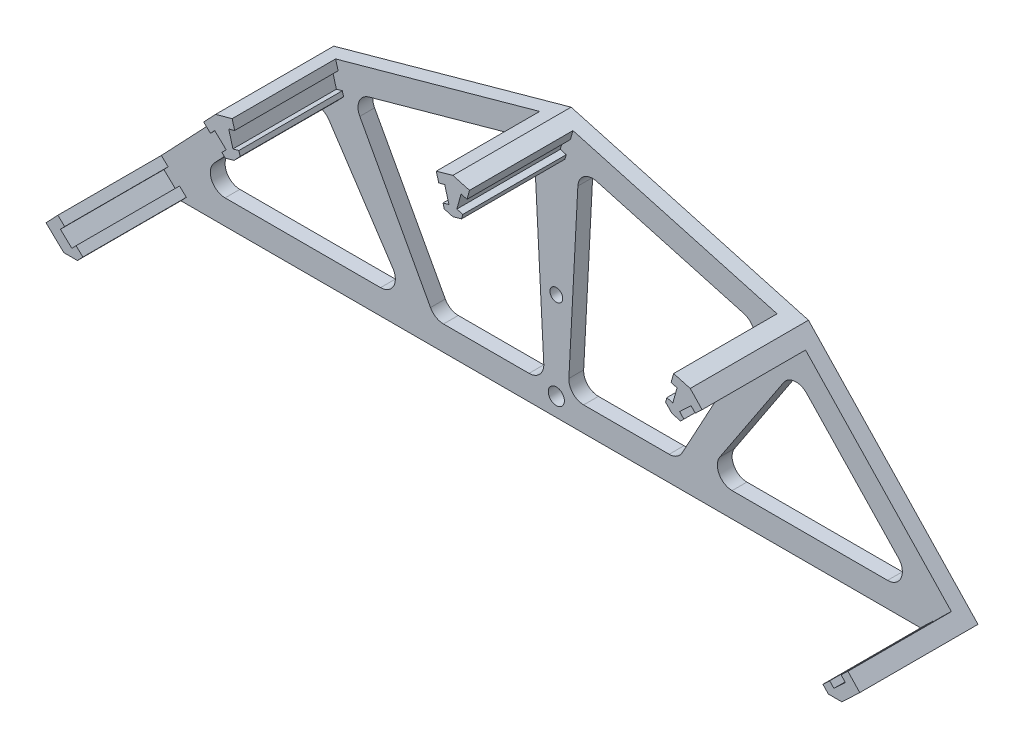
SolidWorks part; units mm, degrees
ref_plane "Front Plane" through (0, 0, 0) normal (0, 0, 1) x (1, 0, 0)
ref_plane "Top Plane" through (0, 0, 0) normal (0, 1, 0) x (1, 0, 0)
ref_plane "Right Plane" through (0, 0, 0) normal (1, 0, 0) x (0, 0, -1)
sketch "Sketch1" plane through (0, 0, 0) normal (0, 0, 1) x (1, 0, 0)
  line L0 (0, -46.7747) -> (0, 46.7747) construction
  line L1 (-82.5993, -2.8559) -> (-78.9724, -6.2977)
  line L2 (82.5993, -2.8559) -> (0, -46.7747) construction
  line L3 (0, 46.7747) -> (48.1815, 33.4128)
  line L4 (48.1815, 33.4128) -> (0, -46.7747) construction
  line L5 (48.1815, 33.4128) -> (82.5993, -2.8559)
  line L6 (82.5993, -2.8559) -> (78.9724, -6.2977)
  line L7 (-48.1815, 33.4128) -> (-82.5993, -2.8559)
  line L8 (-48.1815, 33.4128) -> (0, -46.7747) construction
  line L9 (0, 46.7747) -> (-48.1815, 33.4128)
  line L10 (-82.5993, -2.8559) -> (0, -46.7747) construction
  line L11 (-78.9724, -6.2977) -> (78.9724, -6.2977)
  dimension "D1" = 5
  dimension "D2" = 31
  dimension "D3" = 31
  dimension "D4" = 50
extrude "Boss-Extrude1" add sketch "Sketch1" along normal blind 3
sketch "Sketch2" plane through (0, 0, 3) normal (0, 0, 1) x (1, 0, 0)
  line L0 (-48.1815, 33.4128) -> (-44.8088, 34.3481)
  line L1 (0, 46.7747) -> (-48.1815, 33.4128) construction
  line L2 (-44.8088, 34.3481) -> (-44.3011, 32.5172)
  line L3 (-42.9381, 27.6027) -> (-46.3109, 26.6674)
  line L4 (-46.3109, 26.6674) -> (-48.1815, 33.4128) construction
  line L5 (-5.6614, 41.5726) -> (-1.2328, 42.8007) construction
  line L6 (1.8707, 40.0293) -> (0, 46.7747) construction
  line L7 (-1.502, 39.094) -> (1.8707, 40.0293)
  line L8 (-2.0098, 40.9249) -> (-1.502, 39.094)
  line L9 (-24.0908, 40.0938) -> (-22.238, 33.4128) construction
  line L10 (0, 46.7747) -> (-48.1815, 33.4128) construction
  line L11 (-45.5056, 32.1832) -> (-44.6504, 29.0996)
  line L12 (-44.3011, 32.5172) -> (-45.5056, 32.1832)
  line L13 (-40.6495, 31.8695) -> (-45.078, 30.6414) construction
  line L14 (-43.4459, 29.4336) -> (-44.6504, 29.0996)
  line L15 (-43.4459, 29.4336) -> (-42.9381, 27.6027)
  line L16 (-2.0098, 40.9249) -> (-0.8053, 41.2589)
  line L17 (-2.865, 44.0085) -> (-1.6604, 44.3425)
  line L18 (-1.6604, 44.3425) -> (-0.8053, 41.2589)
  line L19 (-3.3727, 45.8394) -> (-2.865, 44.0085)
  line L20 (0, 46.7747) -> (-3.3727, 45.8394)
  line L21 (0, 46.7747) -> (0, -46.7747) construction
  line L22 (40.6495, 31.8695) -> (45.078, 30.6414) construction
  line L23 (24.0908, 40.0938) -> (22.238, 33.4128) construction
  line L24 (1.502, 39.094) -> (-1.8707, 40.0293)
  line L25 (-1.8707, 40.0293) -> (0, 46.7747) construction
  line L26 (5.6614, 41.5726) -> (1.2328, 42.8007) construction
  line L27 (46.3109, 26.6674) -> (48.1815, 33.4128) construction
  line L28 (42.9381, 27.6027) -> (46.3109, 26.6674)
  line L29 (0, 46.7747) -> (3.3727, 45.8394)
  line L30 (3.3727, 45.8394) -> (2.865, 44.0085)
  line L31 (1.6604, 44.3425) -> (0.8053, 41.2589)
  line L32 (2.865, 44.0085) -> (1.6604, 44.3425)
  line L33 (2.0098, 40.9249) -> (0.8053, 41.2589)
  line L34 (43.4459, 29.4336) -> (42.9381, 27.6027)
  line L35 (43.4459, 29.4336) -> (44.6504, 29.0996)
  line L36 (44.3011, 32.5172) -> (45.5056, 32.1832)
  line L37 (45.5056, 32.1832) -> (44.6504, 29.0996)
  line L38 (2.0098, 40.9249) -> (1.502, 39.094)
  line L39 (44.8088, 34.3481) -> (44.3011, 32.5172)
  line L40 (48.1815, 33.4128) -> (44.8088, 34.3481)
  line L41 (48.1815, 33.4128) -> (0, -46.7747) construction
  line L42 (0, -46.7747) -> (-48.1815, 33.4128) construction
  line L43 (-75.7652, -4.371) -> (-82.5993, -2.8559) construction
  line L44 (-50.355, 26.0379) -> (-47.1915, 29.3715) construction
  line L45 (-65.3904, 15.2784) -> (-60.3613, 10.506) construction
  line L46 (-75.1124, -5.1356) -> (-77.5216, -7.6744)
  line L47 (-77.5216, -7.6744) -> (-82.5993, -2.8559)
  line L48 (-75.3482, -0.2995) -> (-78.5116, -3.6331) construction
  line L49 (-43.1039, 28.5943) -> (-48.1815, 33.4128) construction
  line L50 (-45.5131, 26.0555) -> (-43.1039, 28.5943)
  line L51 (-82.5993, -2.8559) -> (-80.19, -0.3171)
  line L52 (-80.19, -0.3171) -> (-78.8118, -1.625)
  line L53 (-79.6722, -2.5317) -> (-77.351, -4.7344)
  line L54 (-78.8118, -1.625) -> (-79.6722, -2.5317)
  line L55 (-76.4906, -3.8277) -> (-77.351, -4.7344)
  line L56 (-46.8914, 27.3634) -> (-45.5131, 26.0555)
  line L57 (-46.8914, 27.3634) -> (-46.0309, 28.2701)
  line L58 (-49.2126, 29.5661) -> (-48.3521, 30.4728)
  line L59 (-48.3521, 30.4728) -> (-46.0309, 28.2701)
  line L60 (-76.4906, -3.8277) -> (-75.1124, -5.1356)
  line L61 (-50.5908, 30.874) -> (-49.2126, 29.5661)
  line L62 (-48.1815, 33.4128) -> (-50.5908, 30.874)
  line L63 (45.5131, 26.0555) -> (43.1039, 28.5943)
  line L64 (43.1039, 28.5943) -> (48.1815, 33.4128) construction
  line L65 (75.3482, -0.2995) -> (78.5116, -3.6331) construction
  line L66 (77.5216, -7.6744) -> (82.5993, -2.8559)
  line L67 (75.1124, -5.1356) -> (77.5216, -7.6744)
  line L68 (65.3904, 15.2784) -> (60.3613, 10.506) construction
  line L69 (50.355, 26.0379) -> (47.1915, 29.3715) construction
  line L70 (48.1815, 33.4128) -> (50.5908, 30.874)
  line L71 (50.5908, 30.874) -> (49.2126, 29.5661)
  line L72 (76.4906, -3.8277) -> (75.1124, -5.1356)
  line L73 (48.3521, 30.4728) -> (46.0309, 28.2701)
  line L74 (49.2126, 29.5661) -> (48.3521, 30.4728)
  line L75 (46.8914, 27.3634) -> (46.0309, 28.2701)
  line L76 (46.8914, 27.3634) -> (45.5131, 26.0555)
  line L77 (76.4906, -3.8277) -> (77.351, -4.7344)
  line L78 (78.8118, -1.625) -> (79.6722, -2.5317)
  line L79 (79.6722, -2.5317) -> (77.351, -4.7344)
  line L80 (80.19, -0.3171) -> (78.8118, -1.625)
  line L81 (82.5993, -2.8559) -> (80.19, -0.3171)
  line L82 (-40.6495, 31.8695) -> (-47.2462, 30.0401) construction
  point P20 (-40.7831, 32.3513)
  point P94 (-47.2462, 30.0401)
  point P98 (-40.6268, 31.7304)
  dimension "D1" = 7
  dimension "D2" = 22.75
  dimension "D3" = 1.6
  dimension "D4" = 1.25
extrude "Boss-Extrude2" add sketch "Sketch2" along normal blind 21
sketch "Sketch3" plane through (0, 0, 3) normal (0, 0, 1) x (1, 0, 0)
  line L0 (0, -46.7747) -> (-74.2276, -1.2977) construction
  line L1 (-69.421, 3.7674) -> (-50.8282, 23.3601)
  line L2 (-46.1504, 22.9509) -> (-33.1822, 3.3581)
  line L3 (-35.6839, -1.2977) -> (-67.2449, -1.2977)
  line L4 (-25.5437, 0.2708) -> (-39.8978, 26.7078)
  line L5 (-38.063, 31.0302) -> (-8.1664, 39.3213)
  line L6 (-4.3688, 36.5874) -> (-2.5488, 1.8593)
  line L7 (-5.5447, -1.2977) -> (-22.9072, -1.2977)
  line L8 (-48.1815, 33.4128) -> (-82.5993, -2.8559) construction
  line L9 (0, 46.7747) -> (-48.1815, 33.4128) construction
  line L10 (-78.9724, -6.2977) -> (78.9724, -6.2977) construction
  line L11 (-48.1815, 33.4128) -> (0, -46.7747) construction
  line L12 (0, -46.7747) -> (0, 46.7747) construction
  line L13 (-2.5488, 1.8593) -> (0, -46.7747) construction
  line L14 (0, 46.7747) -> (0, 0) construction
  line L15 (5.5447, -1.2977) -> (22.9072, -1.2977)
  line L16 (4.3688, 36.5874) -> (2.5488, 1.8593)
  line L17 (38.063, 31.0302) -> (8.1664, 39.3213)
  line L18 (25.5437, 0.2708) -> (39.8978, 26.7078)
  line L19 (35.6839, -1.2977) -> (67.2449, -1.2977)
  line L20 (46.1504, 22.9509) -> (33.1822, 3.3581)
  line L21 (69.421, 3.7674) -> (50.8282, 23.3601)
  arc A0 (-35.6839, -1.2977) -> (-33.1822, 3.3581) centre (-35.6839, 1.7023) ccw
  arc A1 (-50.8282, 23.3601) -> (-46.1504, 22.9509) centre (-48.652, 21.2951) cw
  arc A2 (-69.421, 3.7674) -> (-67.2449, -1.2977) centre (-67.2449, 1.7023) ccw
  arc A3 (-25.5437, 0.2708) -> (-22.9072, -1.2977) centre (-22.9072, 1.7023) ccw
  arc A4 (-39.8978, 26.7078) -> (-38.063, 31.0302) centre (-37.2613, 28.1393) cw
  arc A5 (-8.1664, 39.3213) -> (-4.3688, 36.5874) centre (-7.3647, 36.4304) cw
  arc A6 (-2.5488, 1.8593) -> (-5.5447, -1.2977) centre (-5.5447, 1.7023) cw
  arc A7 (2.5488, 1.8593) -> (5.5447, -1.2977) centre (5.5447, 1.7023) ccw
  arc A8 (8.1664, 39.3213) -> (4.3688, 36.5874) centre (7.3647, 36.4304) ccw
  arc A9 (39.8978, 26.7078) -> (38.063, 31.0302) centre (37.2613, 28.1393) ccw
  arc A10 (25.5437, 0.2708) -> (22.9072, -1.2977) centre (22.9072, 1.7023) cw
  arc A11 (69.421, 3.7674) -> (67.2449, -1.2977) centre (67.2449, 1.7023) cw
  arc A12 (50.8282, 23.3601) -> (46.1504, 22.9509) centre (48.652, 21.2951) ccw
  arc A13 (35.6839, -1.2977) -> (33.1822, 3.3581) centre (35.6839, 1.7023) cw
  circle A14 centre (0, -2.5545) radius 1.6425
  circle A15 centre (0, 15.2704) radius 1.293
  dimension "D6" = 3
  dimension "D7" = 3
  dimension "D8" = 3
  dimension "D1" = 5
  dimension "D2" = 5
  dimension "D3" = 5
  dimension "D4" = 2.5
  dimension "D5" = 2.5
  dimension "D9" = 3
extrude "Cut-Extrude1" cut sketch "Sketch3" against normal through all
sketch "Sketch5" plane through (0, 0, 24) normal (0, 0, 1) x (1, 0, 0)
  line L0 (-73.6877, -11.8812) -> (-66.4917, 7.1034)
  line L1 (-66.4917, 7.1034) -> (-31.6623, 32.4212)
  line L2 (-31.6623, 32.4212) -> (-32.1393, 38.3933)
  line L3 (97.2019, -18.6925) -> (-73.6877, -11.8812)
  arc A0 (-32.1393, 38.3933) -> (97.2019, -18.6925) centre (47.9525, 44.7906) cw
extrude "Cut-Extrude2" [suppressed] cut sketch "Sketch5" against normal through all
equation "\"D3@Sketch1\"=\"D2@Sketch1\""
equation "\"D5@Sketch3\"=\"D4@Sketch3\""
